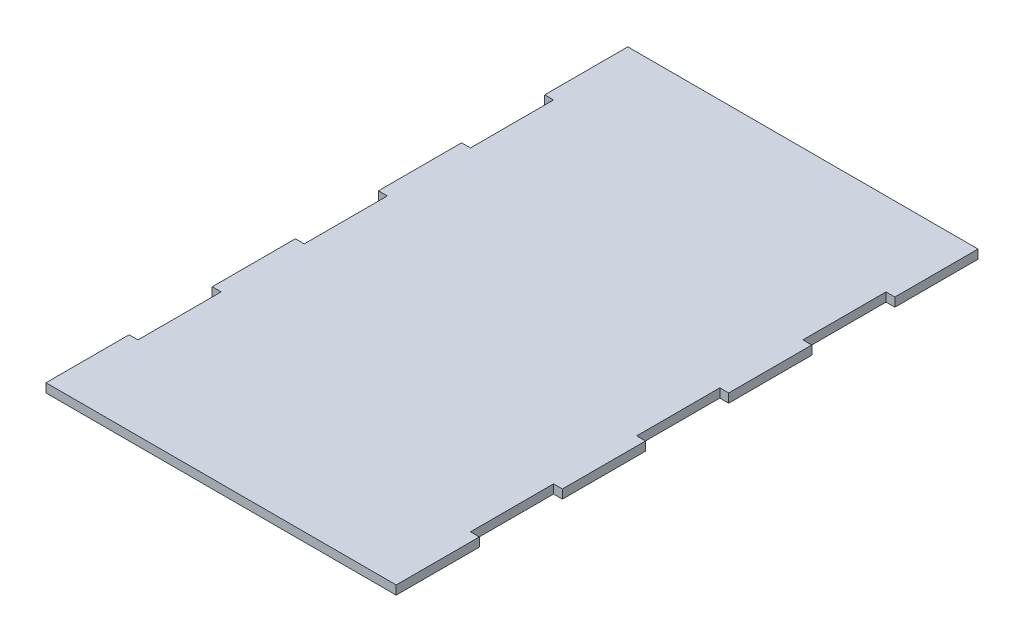
SolidWorks part; units mm, degrees
material "A-Glass Fiber"
ref_plane "Front Plane" through (0, 0, 0) normal (0, 0, 1) x (1, 0, 0)
ref_plane "Top Plane" through (0, 0, 0) normal (0, 1, 0) x (1, 0, 0)
ref_plane "Right Plane" through (0, 0, 0) normal (1, 0, 0) x (0, 0, -1)
sketch "Sketch1" plane through (0, 0, 0) normal (0, 1, 0) x (1, 0, 0)
  line L0 (200.66, 762) -> (200.66, 0) construction
  line L1 (0, 0) -> (401.32, 0)
  line L2 (0, 0) -> (0, 762)
  line L3 (0, 762) -> (401.32, 762)
  line L4 (401.32, 0) -> (401.32, 762)
  line L5 (0, 762) -> (10.16, 762)
  line L6 (0, 762) -> (0, 666.75)
  line L7 (0, 666.75) -> (10.16, 666.75)
  line L8 (10.16, 762) -> (10.16, 666.75)
  line L9 (0, 666.75) -> (10.16, 666.75)
  line L10 (0, 666.75) -> (0, 571.5)
  line L11 (0, 571.5) -> (10.16, 571.5)
  line L12 (10.16, 666.75) -> (10.16, 571.5)
  line L13 (0, 571.5) -> (10.16, 571.5)
  line L14 (0, 571.5) -> (0, 476.25)
  line L15 (0, 476.25) -> (10.16, 476.25)
  line L16 (10.16, 571.5) -> (10.16, 476.25)
  line L17 (0, 476.25) -> (10.16, 476.25)
  line L18 (0, 476.25) -> (0, 381)
  line L19 (0, 381) -> (10.16, 381)
  line L20 (10.16, 476.25) -> (10.16, 381)
  line L21 (0, 381) -> (10.16, 381)
  line L22 (0, 381) -> (0, 285.75)
  line L23 (0, 285.75) -> (10.16, 285.75)
  line L24 (10.16, 381) -> (10.16, 285.75)
  line L25 (0, 285.75) -> (10.16, 285.75)
  line L26 (0, 285.75) -> (0, 190.5)
  line L27 (0, 190.5) -> (10.16, 190.5)
  line L28 (10.16, 285.75) -> (10.16, 190.5)
  line L29 (0, 190.5) -> (10.16, 190.5)
  line L30 (0, 190.5) -> (0, 95.25)
  line L31 (0, 95.25) -> (10.16, 95.25)
  line L32 (10.16, 190.5) -> (10.16, 95.25)
  line L33 (0, 95.25) -> (10.16, 95.25)
  line L34 (0, 95.25) -> (0, 0)
  line L35 (0, 0) -> (10.16, 0)
  line L36 (10.16, 95.25) -> (10.16, 0)
  line L37 (391.16, 95.25) -> (391.16, 0)
  line L38 (401.32, 0) -> (391.16, 0)
  line L39 (401.32, 95.25) -> (401.32, 0)
  line L40 (401.32, 95.25) -> (391.16, 95.25)
  line L41 (391.16, 190.5) -> (391.16, 95.25)
  line L42 (401.32, 95.25) -> (391.16, 95.25)
  line L43 (401.32, 190.5) -> (401.32, 95.25)
  line L44 (401.32, 190.5) -> (391.16, 190.5)
  line L45 (391.16, 285.75) -> (391.16, 190.5)
  line L46 (401.32, 190.5) -> (391.16, 190.5)
  line L47 (401.32, 285.75) -> (401.32, 190.5)
  line L48 (401.32, 285.75) -> (391.16, 285.75)
  line L49 (391.16, 381) -> (391.16, 285.75)
  line L50 (401.32, 285.75) -> (391.16, 285.75)
  line L51 (401.32, 381) -> (401.32, 285.75)
  line L52 (401.32, 381) -> (391.16, 381)
  line L53 (391.16, 476.25) -> (391.16, 381)
  line L54 (401.32, 381) -> (391.16, 381)
  line L55 (401.32, 476.25) -> (401.32, 381)
  line L56 (401.32, 476.25) -> (391.16, 476.25)
  line L57 (391.16, 571.5) -> (391.16, 476.25)
  line L58 (401.32, 476.25) -> (391.16, 476.25)
  line L59 (401.32, 571.5) -> (401.32, 476.25)
  line L60 (401.32, 571.5) -> (391.16, 571.5)
  line L61 (391.16, 666.75) -> (391.16, 571.5)
  line L62 (401.32, 571.5) -> (391.16, 571.5)
  line L63 (401.32, 666.75) -> (401.32, 571.5)
  line L64 (401.32, 666.75) -> (391.16, 666.75)
  line L65 (391.16, 762) -> (391.16, 666.75)
  line L66 (401.32, 666.75) -> (391.16, 666.75)
  line L67 (401.32, 762) -> (401.32, 666.75)
  line L68 (401.32, 762) -> (391.16, 762)
  line L69 (401.32, 0) -> (401.32, 762)
  line L70 (10.16, 666.75) -> (391.16, 666.75)
  dimension "D1" = 381
  dimension "D2" = 762
  dimension "D3" = 10.16
extrude "Boss-Extrude1" add sketch "Sketch1" along normal blind 10.16 contours L0 L3 L8 L12 L16 L20 L24 L28 L32 L36 L1 | L3 L0 L1 L37 L41 L45 L49 L53 L57 L61 L65 | L36 L31 L2 L1 | L20 L15 L2 L19 | L28 L23 L2 L27 | L12 L7 L2 L11 | L4 L40 L37 L1 | L4 L48 L45 L44 | L4 L56 L53 L52 | L4 L64 L61 L60
